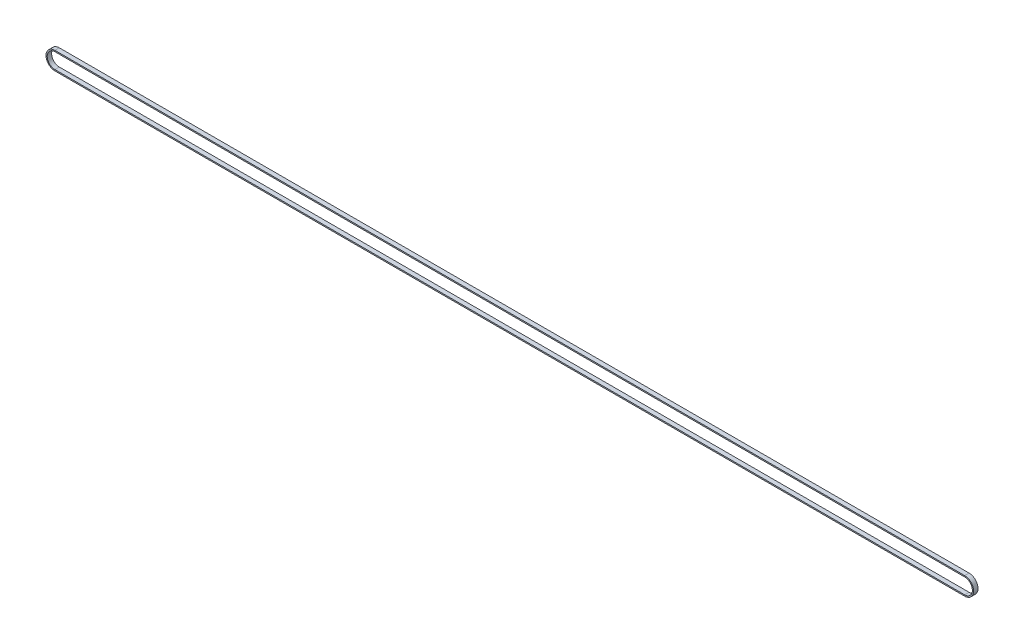
SolidWorks part; units mm, degrees
material "Rubber"
ref_plane "Front Plane" through (0, 0, 0) normal (0, 0, 1) x (1, 0, 0)
ref_plane "Top Plane" through (0, 0, 0) normal (0, 1, 0) x (1, 0, 0)
ref_plane "Right Plane" through (0, 0, 0) normal (1, 0, 0) x (0, 0, -1)
sketch "Sketch1" plane through (0, 0, 0) normal (0, 0, 1) x (1, 0, 0)
  line L0 (0, 0) -> (1032, 0) construction
  line L1 (0, 8.75) -> (1032, 8.75)
  line L2 (1032, -8.75) -> (0, -8.75)
  arc A0 (0, 8.75) -> (0, -8.75) centre (0, 0) ccw
  arc A1 (1032, -8.75) -> (1032, 8.75) centre (1032, 0) ccw
  dimension "D1" = 17.5
  dimension "D2" = 1032
extrude "Extrude-Thin1" add sketch "Sketch1" along normal mid plane 5 thin thin type one direction wall 1.38
